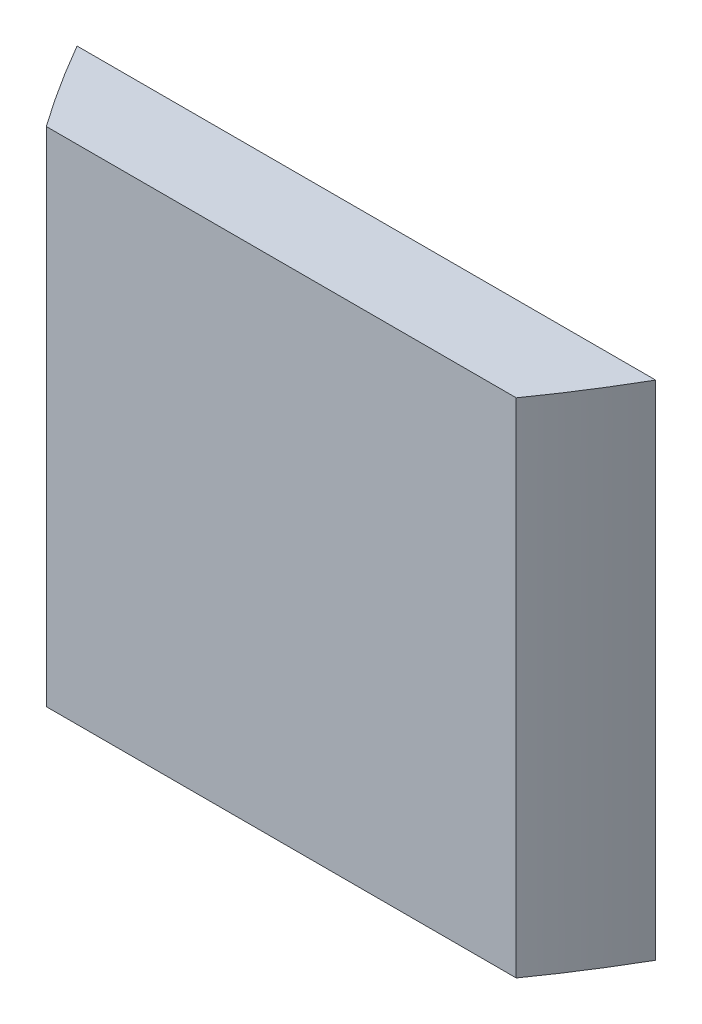
SolidWorks part; units mm, degrees
material "Custom Plastic (2)"
ref_plane "Front Plane" through (0, 0, 0) normal (0, 0, 1) x (1, 0, 0)
ref_plane "Top Plane" through (0, 0, 0) normal (0, 1, 0) x (1, 0, 0)
ref_plane "Right Plane" through (0, 0, 0) normal (1, 0, 0) x (0, 0, -1)
sketch "Sketch1" plane through (0, 0, 0) normal (0, 1, 0) x (1, 0, 0)
  line L0 (-200, 0) -> (200, 0)
  spline S0 degree 2 poles (-225.2396, 53.6645) (0, -453.6645) (225.2396, 53.6645) knots 0 0 0 1 1 1 construction
  spline S1 degree 2 poles (-200, 0) (0, -400) (200, 0) knots 0.056028 0.056028 0.056028 0.943972 0.943972 0.943972
extrude "Boss-Extrude1" add sketch "Sketch1" along normal blind 300
sketch "Sketch2" plane through (0, 300, 0) normal (0, 1, 0) x (1, 0, 0)
  line L0 (200, 0) -> (-200, 0) construction
  line L1 (-222.6767, 47.5766) -> (226.2218, 47.5766)
  line L2 (-222.6767, 47.5766) -> (-222.6767, -50.8)
  line L3 (-222.6767, -50.8) -> (226.2218, -50.8)
  line L4 (226.2218, 47.5766) -> (226.2218, -50.8)
  dimension "D1" = 50.8
extrude "Cut-Extrude1" cut sketch "Sketch2" against normal blind 350
sketch "Sketch3" plane through (0, 300, 0) normal (0, 1, 0) x (1, 0, 0)
  line L0 (-172.7426, -50.8) -> (172.7426, -50.8) construction
  line L1 (-221.4173, -101.6) -> (219.8863, -101.6)
  line L2 (-221.4173, -101.6) -> (-221.4173, -239.3878)
  line L3 (-221.4173, -239.3878) -> (219.8863, -239.3878)
  line L4 (219.8863, -101.6) -> (219.8863, -239.3878)
  dimension "D1" = 50.8
extrude "Cut-Extrude2" cut sketch "Sketch3" against normal blind 350
